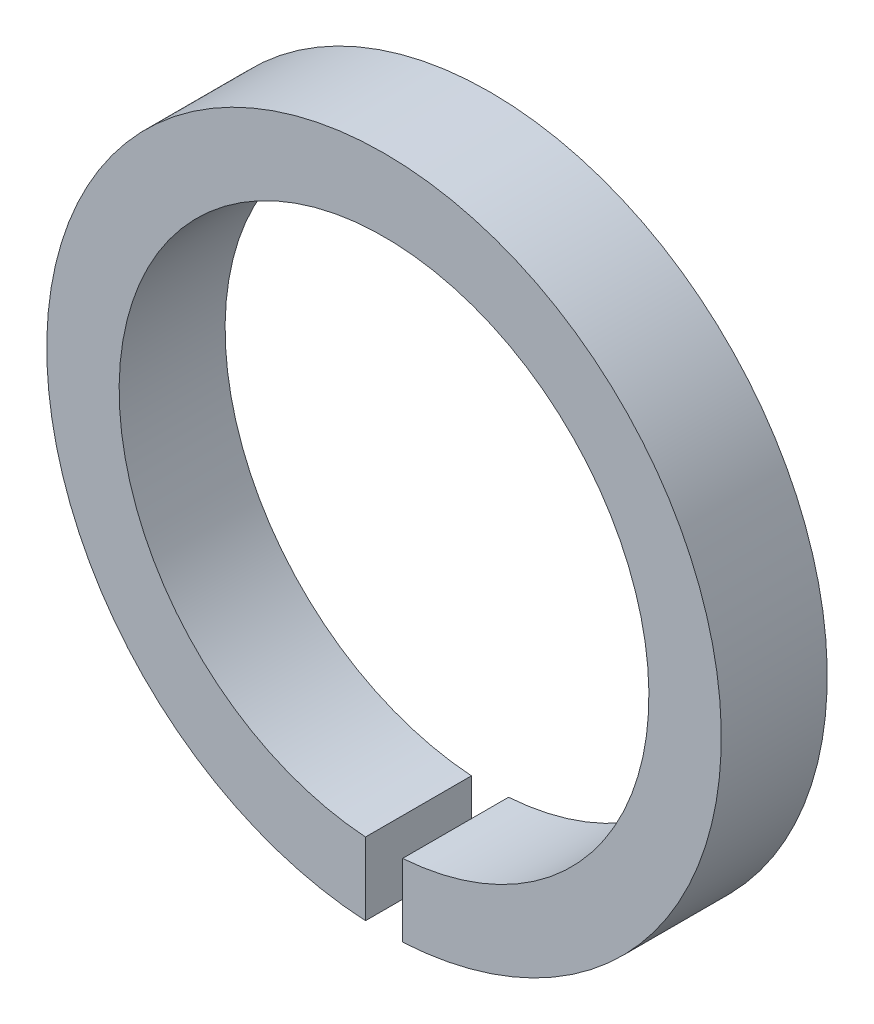
SolidWorks part; units mm, degrees
ref_plane "Front Plane" through (0, 0, 0) normal (0, 0, 1) x (1, 0, 0)
ref_plane "Top Plane" through (0, 0, 0) normal (0, 1, 0) x (1, 0, 0)
ref_plane "Right Plane" through (0, 0, 0) normal (1, 0, 0) x (0, 0, -1)
sketch "Sketch1" plane through (0, 0, 0) normal (0, 0, 1) x (1, 0, 0)
  circle A0 centre (0, 0) radius 12.7
  circle A1 centre (0, 0) radius 16.1704
  dimension "D1" = 25.4
extrude "Boss-Extrude1" add sketch "Sketch1" along normal blind 5.08
sketch "Sketch2" plane through (0, 0, 5.08) normal (0, 0, 1) x (1, 0, 0)
  line L1 (-0.889, -0.9601) -> (0.889, -0.9601)
  line L2 (-0.889, -0.9601) -> (-0.889, -16.8504)
  line L3 (-0.889, -16.8504) -> (0.889, -16.8504)
  line L4 (0.889, -0.9601) -> (0.889, -16.8504)
  point P4 (0, -0.9601)
  dimension "D1" = 1.778
extrude "Cut-Extrude1" cut sketch "Sketch2" against normal blind 5.08
